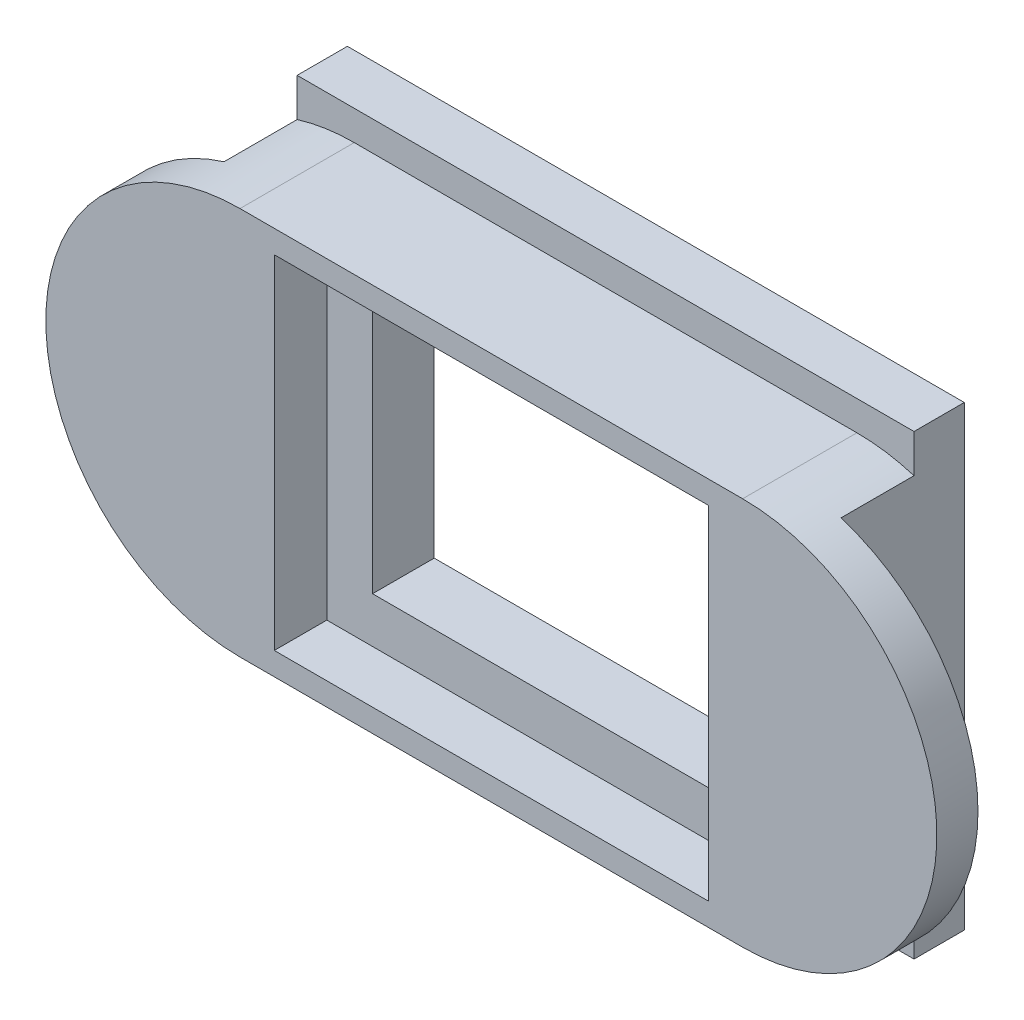
SolidWorks part; units mm, degrees
ref_plane "Спереди" through (0, 0, 0) normal (0, 0, 1) x (1, 0, 0)
ref_plane "Сверху" through (0, 0, 0) normal (0, 1, 0) x (1, 0, 0)
ref_plane "Справа" through (0, 0, 0) normal (1, 0, 0) x (0, 0, -1)
sketch "Эскиз1" plane through (0, 0, 0) normal (0, 0, 1) x (1, 0, 0)
  line L0 (-11, 0) -> (11, 0) construction
  line L1 (-11, 8.5) -> (11, 8.5)
  line L2 (-11, -8.5) -> (11, -8.5)
  line L4 (-7.5, -5.5) -> (7.5, -5.5)
  line L5 (-7.5, -5.5) -> (-7.5, 5.5)
  line L6 (-7.5, 5.5) -> (7.5, 5.5)
  line L7 (7.5, -5.5) -> (7.5, 5.5)
  line L8 (-7.5, -5.5) -> (7.5, 5.5) construction
  line L9 (-7.5, 5.5) -> (7.5, -5.5) construction
  arc A0 (-11, 8.5) -> (-11, -8.5) centre (-11, 0) ccw
  arc A1 (11, -8.5) -> (11, 8.5) centre (11, 0) ccw
  point P3 (0, 0)
  point P9 (0, 0)
  dimension "D1" = 17
  dimension "D2" = 22
  dimension "D3" = 15
  dimension "D4" = 11
extrude "Бобышка-Вытянуть1" add sketch "Эскиз1" along normal blind 5
sketch "Эскиз2" plane through (0, 0, 5) normal (0, 0, 1) x (1, 0, 0)
  line L1 (-9.5, -7.5) -> (9.5, -7.5)
  line L2 (-9.5, -7.5) -> (-9.5, 7.5)
  line L3 (-9.5, 7.5) -> (9.5, 7.5)
  line L4 (9.5, -7.5) -> (9.5, 7.5)
  line L5 (-9.5, -7.5) -> (9.5, 7.5) construction
  line L6 (-9.5, 7.5) -> (9.5, -7.5) construction
  point P0 (0, 0)
  dimension "D1" = 19
  dimension "D2" = 15
extrude "Вырез-Вытянуть1" cut sketch "Эскиз2" against normal blind 2.3
sketch "Эскиз3" plane through (0, 0, 0) normal (0, 0, -1) x (-1, 0, 0)
  line L0 (11, -8.5) -> (-11, -8.5) construction
  line L1 (13.5, 8.5) -> (-13.5, 8.5)
  line L2 (13.5, 8.5) -> (13.5, -8.5)
  line L3 (13.5, -8.5) -> (-13.5, -8.5)
  line L4 (-13.5, 8.5) -> (-13.5, -8.5)
  line L5 (13.5, 8.5) -> (-13.5, -8.5) construction
  line L6 (13.5, -8.5) -> (-13.5, 8.5) construction
  point P0 (0, 0)
  dimension "D1" = 27
extrude "Вырез-Вытянуть2" cut sketch "Эскиз3" against normal offset from surface (3.2 mm away) 1.8 flip side to cut up to face at (0, 0, 5)
sketch "Эскиз4" plane through (0, 0, 0) normal (0, 0, -1) x (-1, 0, 0)
  line L0 (-13.5, 8.124) -> (-13.5, -8.124) construction
  line L1 (-13.5, 9.8) -> (13.5, 9.8)
  line L2 (-13.5, 9.8) -> (-13.5, -10.2)
  line L3 (-13.5, -10.2) -> (13.5, -10.2)
  line L4 (13.5, 9.8) -> (13.5, -10.2)
  line L5 (13.5, -8.124) -> (13.5, 8.124) construction
  line L6 (-11, 8.5) -> (11, 8.5) construction
  dimension "D1" = 20
  dimension "D2" = 1.3
extrude "Бобышка-Вытянуть2" add sketch "Эскиз4" along normal blind 2.2
sketch "Эскиз5" plane through (0, 0, 0) normal (0, 0, 1) x (1, 0, 0)
  line L0 (7.5, 5.5) -> (-7.5, 5.5) construction
  line L1 (7.5, -5.5) -> (7.5, 5.5) construction
  line L2 (-7.5, -5.5) -> (7.5, -5.5) construction
  line L3 (-7.5, 5.5) -> (-7.5, -5.5) construction
  line L4 (7.5, 5.5) -> (-7.5, 5.5)
  line L5 (7.5, -5.5) -> (7.5, 5.5)
  line L6 (-7.5, -5.5) -> (7.5, -5.5)
  line L7 (-7.5, 5.5) -> (-7.5, -5.5)
extrude "Вырез-Вытянуть3" cut sketch "Эскиз5" against normal through all draft 57 draft outward yes
